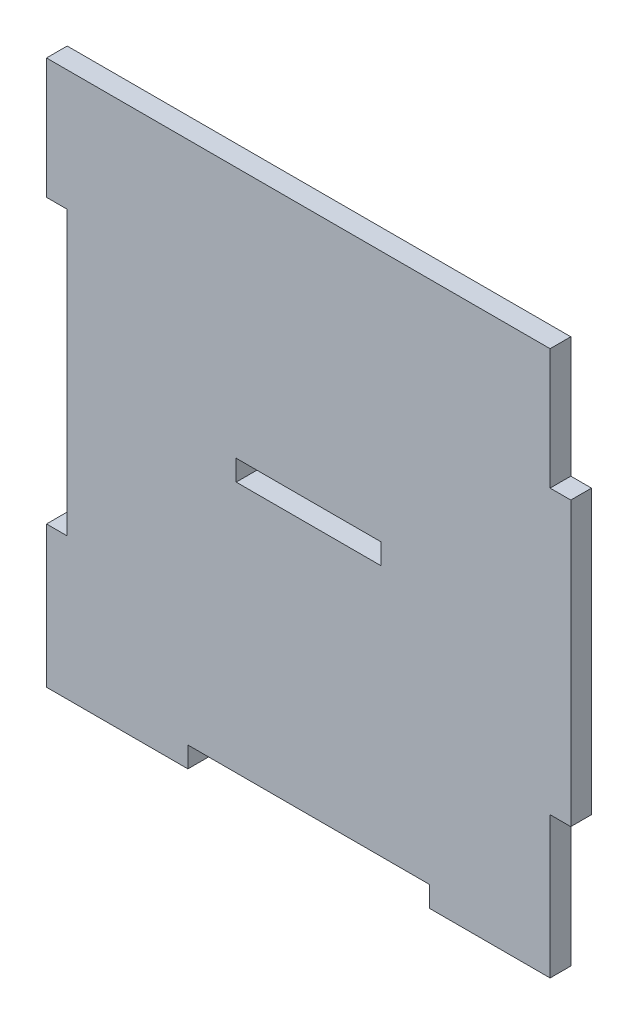
SolidWorks part; units mm, degrees
ref_plane "Front Plane" through (0, 0, 0) normal (0, 0, 1) x (1, 0, 0)
ref_plane "Top Plane" through (0, 0, 0) normal (0, 1, 0) x (1, 0, 0)
ref_plane "Right Plane" through (0, 0, 0) normal (1, 0, 0) x (0, 0, -1)
sketch "Sketch1" plane through (0, 0, 0) normal (0, 0, 1) x (1, 0, 0)
  line L0 (0, 35) -> (0, -38) construction
  line L5 (-35, 38) -> (-17.5, 38)
  line L6 (-35, 20.5) -> (-35, -20.5)
  line L7 (-17.5, -38) -> (17.5, -38)
  line L24 (35, 38) -> (35, 20.5)
  line L25 (-35, 38) -> (35, -38) construction
  line L26 (-35, -38) -> (35, 38) construction
  line L27 (-35, 0) -> (35, 0) construction
  line L31 (-35, -20.5) -> (-38, -20.5)
  line L32 (-35, 20.5) -> (-38, 20.5)
  line L33 (-38, 20.5) -> (-38, 38)
  line L34 (-38, 38) -> (-35, 38)
  line L35 (-38, -20.5) -> (-38, -38)
  line L36 (-17.5, 38) -> (17.5, 38)
  line L37 (35, -38) -> (35, -41)
  line L38 (35, -20.5) -> (38, -20.5)
  line L39 (35, -41) -> (17.5, -41)
  line L40 (35, 20.5) -> (38, 20.5)
  line L41 (17.5, -41) -> (17.5, -38)
  line L42 (-17.5, -38) -> (-17.5, -41)
  line L43 (38, 20.5) -> (38, -20.5)
  line L45 (-35, -41) -> (-17.5, -41)
  line L46 (17.5, 38) -> (35, 38)
  line L47 (35, -20.5) -> (35, -38)
  line L48 (-38, -38) -> (-38, -41)
  line L49 (-38, -41) -> (-35, -41)
  point P0 (0, 0)
  dimension "D1" = 76
  dimension "D2" = 70
  dimension "D3" = 17.5
  dimension "D4" = 17.5
  dimension "D5" = 3
  dimension "D6" = 3
  dimension "D7" = 3
extrude "Boss-Extrude1" add sketch "Sketch1" along normal blind 3
sketch "Sketch2" plane through (0, 0, 3) normal (0, 0, 1) x (1, 0, 0)
  line L1 (-10.5, -1.5) -> (10.5, -1.5)
  line L2 (-10.5, -1.5) -> (-10.5, 1.5)
  line L3 (-10.5, 1.5) -> (10.5, 1.5)
  line L4 (10.5, -1.5) -> (10.5, 1.5)
  line L5 (-10.5, -1.5) -> (10.5, 1.5) construction
  line L6 (-10.5, 1.5) -> (10.5, -1.5) construction
  point P0 (0, 0)
  dimension "D1" = 21
  dimension "D2" = 3
extrude "Cut-Extrude1" cut sketch "Sketch2" against normal blind 3
